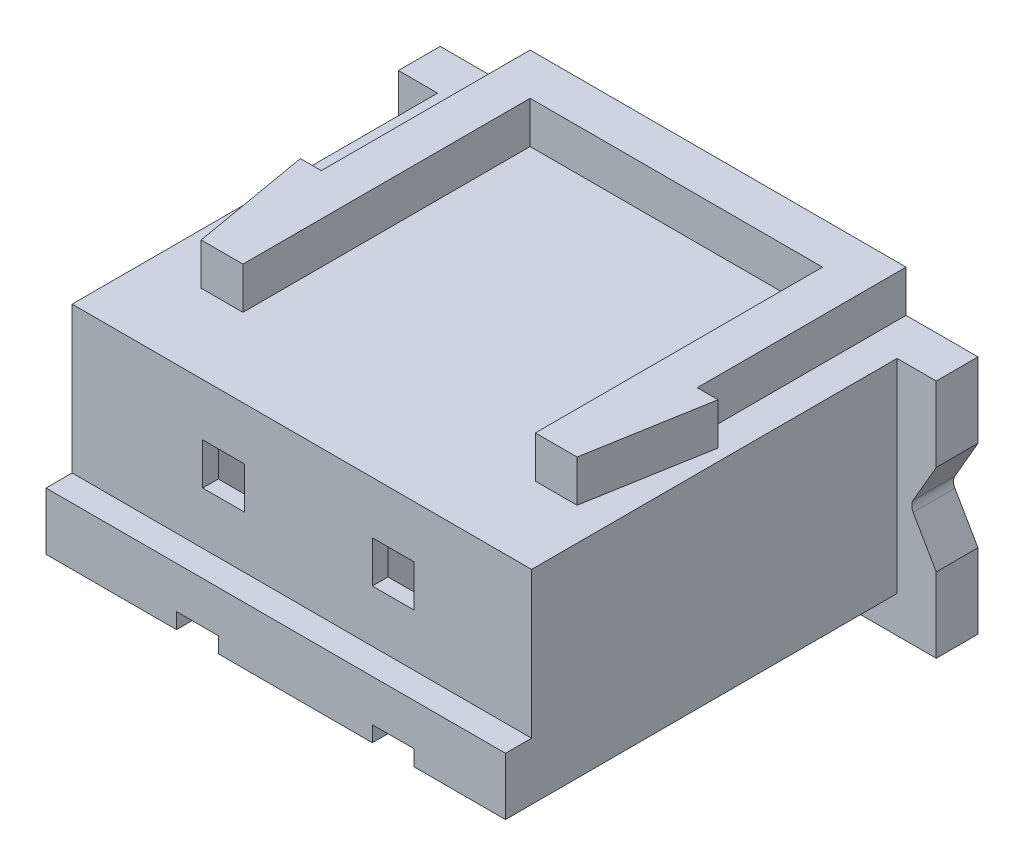
SolidWorks part; units mm, degrees
ref_plane "Front Plane" through (0, 0, 0) normal (0, 0, 1) x (1, 0, 0)
ref_plane "Top Plane" through (0, 0, 0) normal (0, 1, 0) x (1, 0, 0)
ref_plane "Right Plane" through (0, 0, 0) normal (1, 0, 0) x (0, 0, -1)
sketch "Sketch1" plane through (0, 0, 0) normal (0, 0, 1) x (1, 0, 0)
  line L1 (-4.4, -2.15) -> (4.4, -2.15)
  line L2 (-4.4, -2.15) -> (-4.4, 2.15)
  line L3 (-4.4, 2.15) -> (4.4, 2.15)
  line L4 (4.4, -2.15) -> (4.4, 2.15)
  line L5 (-4.4, -2.15) -> (4.4, 2.15) construction
  line L6 (-4.4, 2.15) -> (4.4, -2.15) construction
  point P0 (0, 0)
  dimension "D1" = 4.3
  dimension "D2" = 8.8
extrude "Boss-Extrude1" add sketch "Sketch1" along normal blind 7
sketch "Sketch2" plane through (0, 0, 0) normal (0, 0, -1) x (-1, 0, 0)
  line L0 (0, 0) -> (0, 2.15) construction
  line L1 (-5.15, 2.15) -> (5.15, 2.15)
  line L2 (-5.15, 2.15) -> (-5.15, -2.45)
  line L3 (-5.15, -2.45) -> (5.15, -2.45)
  line L4 (5.15, 2.15) -> (5.15, -2.45)
  dimension "D1" = 10.3
  dimension "D2" = 4.6
extrude "Boss-Extrude2" add sketch "Sketch2" along normal blind 0.8
sketch "Sketch3" plane through (0, 0, 0) normal (0, 0, 1) x (1, 0, 0)
  line L1 (5.15, 2.15) -> (5.15, -2.45) construction
  line L2 (4.65, -0.15) -> (5.15, -1.016)
  line L3 (4.65, -0.15) -> (5.15, 0.716)
  line L4 (5.15, -0.15) -> (4.65, -0.15) construction
  line L5 (5.15, 0.716) -> (5.15, -1.016)
  dimension "D1" = 60
  dimension "D2" = 0.5
  dimension "D3" = 60
extrude "Cut-Extrude1" cut sketch "Sketch3" against normal blind 1
fillet "Fillet1" radius 0.2 1 edges at (4.65, -0.15, -0.4)
sketch "Sketch4" plane through (0, 0, 7) normal (0, 0, 1) x (1, 0, 0)
  line L0 (-4.4, 2.15) -> (-4.4, -2.15) construction
  line L1 (-4.4, -0.65) -> (4.4, -0.65)
  line L2 (-4.4, -0.65) -> (-4.4, -2.15)
  line L3 (-4.4, -2.15) -> (4.4, -2.15)
  line L4 (4.4, -0.65) -> (4.4, -2.15)
  dimension "D1" = 1.5
extrude "Boss-Extrude3" add sketch "Sketch4" along normal blind 0.5
sketch "Sketch5" plane through (0, 0, 7.5) normal (0, 0, 1) x (1, 0, 0)
  line L0 (-4.4, -2.15) -> (4.4, -2.15) construction
  line L1 (-1.9, -1.45) -> (-1.1, -1.45)
  line L2 (-1.9, -1.45) -> (-1.9, -2.15)
  line L3 (-1.9, -2.15) -> (-1.1, -2.15)
  line L4 (-1.1, -1.45) -> (-1.1, -2.15)
  line L5 (-4.4, -0.65) -> (-4.4, -2.15) construction
  line L6 (2.65, -1.45) -> (2.65, -2.15)
  line L7 (1.85, -1.45) -> (2.65, -1.45)
  line L8 (1.85, -1.45) -> (1.85, -2.15)
  line L9 (1.85, -2.15) -> (2.65, -2.15)
  line L10 (4.4, -2.15) -> (4.4, -0.65) construction
  dimension "D1" = 0.8
  dimension "D2" = 2.5
  dimension "D3" = 2
  dimension "D4" = 1.75
extrude "Cut-Extrude2" cut sketch "Sketch5" against normal blind 3.2
sketch "Sketch6" plane through (0, 0, 7) normal (0, 0, 1) x (1, 0, 0)
  line L0 (-4.4, 2.15) -> (-4.4, -0.65) construction
  line L1 (-1.9, 1.15) -> (-1.1, 1.15)
  line L2 (-1.9, 1.15) -> (-1.9, 0.35)
  line L3 (-1.9, 0.35) -> (-1.1, 0.35)
  line L4 (-1.1, 1.15) -> (-1.1, 0.35)
  line L5 (1.35, 1.15) -> (2.15, 1.15)
  line L6 (1.35, 1.15) -> (1.35, 0.35)
  line L7 (1.35, 0.35) -> (2.15, 0.35)
  line L8 (2.15, 1.15) -> (2.15, 0.35)
  line L9 (5.15, 2.15) -> (5.15, 0.716) construction
  line L18 (4.4, 2.15) -> (-4.4, 2.15) construction
  dimension "D1" = 0.8
  dimension "D2" = 0.8
  dimension "D3" = 2.5
  dimension "D5" = 3
  dimension "D6" = 1
  dimension "D4" = 2
extrude "Cut-Extrude3" cut sketch "Sketch6" against normal blind 10
sketch "Sketch7" plane through (0, 2.15, 0) normal (0, 1, 0) x (1, 0, 0)
  line L0 (-3.428, -5.5) -> (-3.828, -3.2)
  line L1 (-3.828, -3.2) -> (-3.428, -3.2)
  line L2 (-3.428, -3.2) -> (-3.428, 0.8)
  line L3 (-5.15, 0.8) -> (5.15, 0.8) construction
  line L4 (-3.428, 0.8) -> (3.772, 0.8)
  line L5 (3.772, 0.8) -> (3.772, -3.2)
  line L6 (3.772, -3.2) -> (4.172, -3.2)
  line L7 (4.172, -3.2) -> (3.772, -5.5)
  line L8 (3.772, -5.5) -> (2.972, -5.5)
  line L9 (2.972, -5.5) -> (2.972, 0)
  line L10 (2.972, 0) -> (-2.628, 0)
  line L11 (-2.628, 0) -> (-2.628, -5.5)
  line L12 (-2.628, -5.5) -> (-3.428, -5.5)
  dimension "D1" = 0.8
  dimension "D2" = 0.8
  dimension "D3" = 0.8
  dimension "D4" = 0.8
  dimension "D5" = 1.2
  dimension "D6" = 4
  dimension "D7" = 2.3
  dimension "D8" = 4
  dimension "D9" = 1.2
  dimension "D10" = 0.8
  dimension "D11" = 8
extrude "Boss-Extrude4" add sketch "Sketch7" along normal blind 0.8
sketch "Sketch8" plane through (0, 0, -0.8) normal (0, 0, -1) x (-1, 0, 0)
  line L1 (2.6, 1.7464) -> (0.4, 1.7464)
  line L2 (2.6, 1.7464) -> (2.6, -1.0536)
  line L3 (1.9, -1.4536) -> (1.1, -1.4536)
  line L4 (0.4, 1.7464) -> (0.4, -1.0536)
  line L5 (2.6, -1.0536) -> (1.9, -1.0536)
  line L6 (1.9, -1.0536) -> (1.9, -1.4536)
  line L7 (1.1, -1.4536) -> (1.1, -1.0536)
  line L8 (1.1, -1.0536) -> (0.4, -1.0536)
  line L9 (-1.15, 1.7464) -> (-3.35, 1.7464)
  line L10 (-1.15, 1.7464) -> (-1.15, -1.0536)
  line L11 (1.1, 1.15) -> (1.9, 0.35) construction
  line L12 (1.9, 0.35) -> (1.9, 1.15) construction
  line L13 (0.4, 1.7464) -> (2.6, -1.0536) construction
  line L14 (2.6, -1.0536) -> (2.6414, -1.0458) construction
  line L15 (-1.85, -1.4536) -> (-2.65, -1.4536)
  line L16 (-3.35, 1.7464) -> (-3.35, -1.0536)
  line L17 (-1.15, -1.0536) -> (-1.85, -1.0536)
  line L18 (-1.85, -1.0536) -> (-1.85, -1.4536)
  line L19 (-2.65, -1.4536) -> (-2.65, -1.0536)
  line L20 (-2.65, -1.0536) -> (-3.35, -1.0536)
  line L21 (-5.15, 2.15) -> (-5.15, 0.716) construction
  line L22 (-3.35, 1.7464) -> (-1.15, -1.0536) construction
  line L23 (-1.15, -1.0536) -> (-1.1086, -1.0458) construction
  line L24 (-2.65, 1.15) -> (-1.85, 0.35) construction
  point P4 (-2.25, 0.75)
  point P12 (0, 0)
  point P16 (1.5, 0.75)
  point P18 (1.5, 0.3464)
  point P31 (-2.25, 0.3464)
  dimension "D1" = 2.8
  dimension "D2" = 2.2
  dimension "D3" = 2
  dimension "D4" = 0.4
  dimension "D5" = 0.7
  dimension "D6" = 0.7
  dimension "D7" = 1.8
extrude "Cut-Extrude4" cut sketch "Sketch8" against normal blind 7.5
sketch "Sketch9" plane through (0, -2.15, 0) normal (0, -1, 0) x (1, 0, 0)
  line L12 (2.65, 7.5) -> (2.65, 4.3)
  line L13 (2.65, 7.5) -> (2.65, 4.3)
  line L27 (1.85, 4.3) -> (1.85, 7.5)
  line L28 (2.65, 4.3) -> (1.85, 4.3)
  line L30 (1.85, 7.5) -> (-1.1, 7.5)
  line L31 (-1.1, 7.5) -> (-1.1, 4.3)
  line L32 (-1.1, 4.3) -> (-1.9, 4.3)
  line L33 (-1.9, 4.3) -> (-1.9, 7.5)
  line L34 (-1.9, 7.5) -> (-4.4, 7.5)
  line L35 (-4.4, 7.5) -> (-4.4, 0)
  line L36 (-4.4, 0) -> (4.4, 0)
  line L37 (4.4, 0) -> (4.4, 7.5)
  line L38 (4.4, 7.5) -> (2.65, 7.5)
  line L47 (1.85, 4.3) -> (1.85, 7.5)
  line L48 (2.65, 4.3) -> (1.85, 4.3)
  line L50 (1.85, 7.5) -> (-1.1, 7.5)
  line L51 (-1.1, 7.5) -> (-1.1, 4.3)
  line L52 (-1.1, 4.3) -> (-1.9, 4.3)
  line L53 (-1.9, 4.3) -> (-1.9, 7.5)
  line L54 (-1.9, 7.5) -> (-4.4, 7.5)
  line L55 (-4.4, 7.5) -> (-4.4, 0)
  line L56 (-4.4, 0) -> (4.4, 0)
  line L57 (4.4, 0) -> (4.4, 7.5)
  line L58 (4.4, 7.5) -> (2.65, 7.5)
  dimension "D1" = 0
extrude "Cut-Extrude5" cut sketch "Sketch9" against normal blind 0.4
sketch "Sketch10" plane through (0, 0, -0.8) normal (0, 0, -1) x (-1, 0, 0)
  line L0 (-5.4156, -2.1633) -> (5.5527, -2.1633) construction
  text T0 "                1                 2" font "Century Gothic" height 0.5
extrude "Boss-Extrude5" add sketch "Sketch10" along normal blind 0.1
